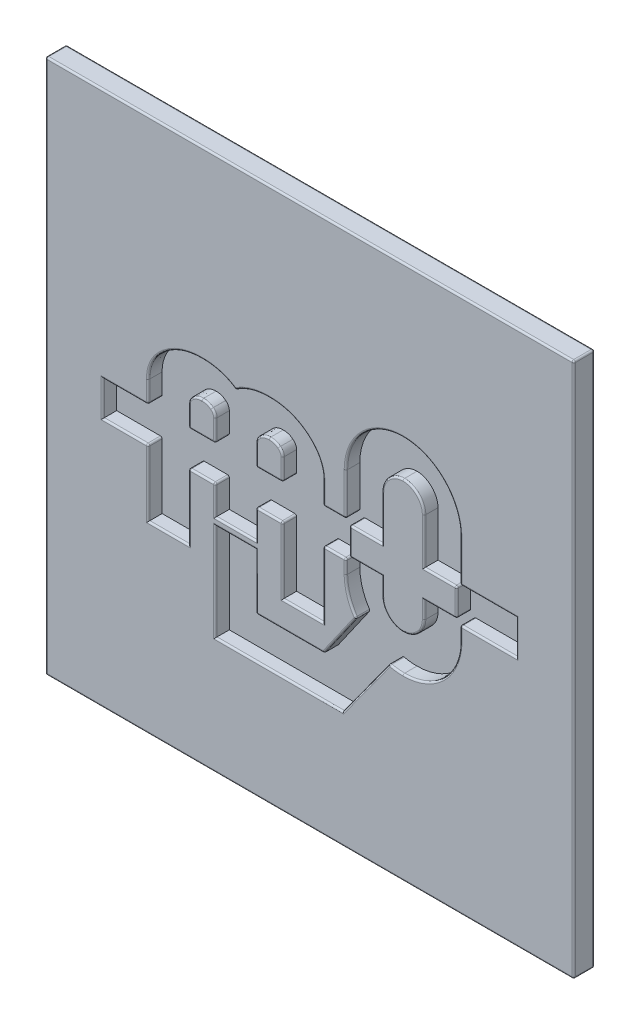
SolidWorks part; units mm, degrees
material "ABS"
ref_plane "Plano frontal" through (0, 0, 0) normal (0, 0, 1) x (1, 0, 0)
ref_plane "Plano superior" through (0, 0, 0) normal (0, 1, 0) x (1, 0, 0)
ref_plane "Plano direito" through (0, 0, 0) normal (1, 0, 0) x (0, 0, -1)
sketch "Model" plane through (0, 0, 0) normal (0, 0, 1) x (1, 0, 0)
  line L0 (10.7309, -25.7678) -> (10.7309, -42.8732)
  line L1 (10.7309, -42.8732) -> (15.5406, -42.8732)
  line L2 (15.5406, -42.8732) -> (15.5406, -25.7678)
  line L3 (20.3712, -25.7678) -> (20.3712, -37.5277)
  line L4 (20.3712, -37.5277) -> (25.1993, -37.5277)
  line L5 (25.1993, -37.5277) -> (25.1993, -25.7678)
  line L6 (30.03, -25.7678) -> (30.03, -42.8732)
  line L7 (30.03, -42.8732) -> (34.8396, -42.8732)
  line L8 (34.8396, -42.8732) -> (34.8396, -25.7678)
  line L9 (39.1028, -22.8429) -> (39.1028, -29.3604)
  line L10 (39.1028, -29.3604) -> (43.7804, -29.3604)
  line L11 (43.7804, -29.3604) -> (43.7804, -22.8429)
  line L12 (49.8174, -22.8429) -> (49.8174, -29.3604)
  line L13 (49.8174, -29.3604) -> (54.495, -29.3604)
  line L14 (54.495, -29.3604) -> (54.495, -22.8429)
  line L15 (43.7804, -35.841) -> (43.7804, -33.3385)
  line L16 (43.7804, -33.3385) -> (39.1028, -33.3385)
  line L17 (39.1028, -33.3385) -> (39.1028, -35.841)
  line L18 (54.495, -35.841) -> (54.495, -33.3385)
  line L19 (54.495, -33.3385) -> (49.8174, -33.3385)
  line L20 (49.8174, -33.3385) -> (49.8174, -35.841)
  line L21 (39.1028, -29.3604) -> (39.1028, -33.3385)
  line L22 (39.1028, -33.3385) -> (4.2108, -33.3385)
  line L23 (4.2108, -33.3385) -> (4.2108, -29.3604)
  line L24 (4.2108, -29.3604) -> (39.1028, -29.3604)
  line L25 (62.5568, -29.3604) -> (62.5568, -33.3385)
  line L26 (62.5568, -33.3385) -> (54.495, -33.3385)
  line L27 (54.495, -33.3385) -> (54.495, -29.3604)
  line L28 (54.495, -29.3604) -> (62.5568, -29.3604)
  line L29 (47.9644, -38.6153) -> (44.6225, -43.2216)
  line L30 (44.6225, -43.2216) -> (37.8938, -52.503)
  line L31 (37.8938, -52.503) -> (20.3712, -52.5003)
  line L32 (20.3712, -52.5003) -> (20.3712, -39.5946)
  line L33 (20.3712, -39.5946) -> (25.1888, -39.5946)
  line L34 (25.1888, -39.5946) -> (25.1888, -47.6142)
  line L35 (25.1888, -47.6142) -> (35.716, -47.6142)
  line L36 (35.716, -47.6142) -> (40.6893, -40.508)
  line L37 (40.6893, -40.508) -> (43.791, -36.0759)
  line L38 (47.9644, -38.6153) -> (44.6225, -43.2216)
  line L39 (40.6893, -40.508) -> (43.791, -36.0759)
  line L40 (25.2002, -33.3389) -> (20.3706, -33.3389)
  line L41 (20.3706, -33.3389) -> (20.3706, -29.3615)
  line L42 (20.3706, -29.3615) -> (25.2002, -29.3615)
  line L43 (25.2002, -29.3615) -> (25.2002, -33.3389)
  line L44 (4.2108, -31.3495) -> (62.5568, -31.3495) construction
  line L50 (-4.5162, -69.7495) -> (71.2838, -69.7495)
  line L51 (-4.5162, -69.7495) -> (-4.5162, 7.0505)
  line L52 (-4.5162, 7.0505) -> (71.2838, 7.0505)
  line L53 (71.2838, -69.7495) -> (71.2838, 7.0505)
  line L54 (-4.5162, -69.7495) -> (71.2838, 7.0505) construction
  line L55 (-4.5162, 7.0505) -> (71.2838, -69.7495) construction
  spline S0 degree 3 poles (32.7226, -21.5653) (31.3129, -20.4065) (29.605, -19.8257) (27.6041, -19.8257) knots 0 0 0 0 1 1 1 1
  spline S1 degree 3 poles (27.6041, -19.8257) (25.751, -19.8257) (24.1408, -20.3325) (22.7761, -21.3436) knots 1 1 1 1 2 2 2 2
  spline S2 degree 3 poles (22.7761, -21.3436) (21.4245, -20.3325) (19.8196, -19.8257) (17.9665, -19.8257) knots 2 2 2 2 3 3 3 3
  spline S3 degree 3 poles (17.9665, -19.8257) (15.9655, -19.8257) (14.255, -20.4091) (12.8375, -21.5732) knots 3 3 3 3 4 4 4 4
  spline S4 degree 3 poles (12.8375, -21.5732) (11.4332, -22.7268) (10.7309, -24.1232) (10.7309, -25.7678) knots 4 4 4 4 5 5 5 5
  spline S5 degree 3 poles (15.5406, -25.7678) (15.5406, -25.2213) (15.7755, -24.7567) (16.2454, -24.3713) knots 8 8 8 8 9 9 9 9
  spline S6 degree 3 poles (16.2454, -24.3713) (16.7179, -23.9859) (17.2907, -23.7906) (17.9665, -23.7906) knots 9 9 9 9 10 10 10 10
  spline S7 degree 3 poles (17.9665, -23.7906) (18.6291, -23.7906) (19.1992, -23.9833) (19.6744, -24.3634) knots 10 10 10 10 11 11 11 11
  spline S8 degree 3 poles (19.6744, -24.3634) (20.139, -24.7541) (20.3712, -25.2213) (20.3712, -25.7678) knots 11 11 11 11 12 12 12 12
  spline S9 degree 3 poles (25.1993, -25.7678) (25.1993, -25.2213) (25.4343, -24.7567) (25.9068, -24.3713) knots 15 15 15 15 16 16 16 16
  spline S10 degree 3 poles (25.9068, -24.3713) (26.3766, -23.9859) (26.9416, -23.7906) (27.6041, -23.7906) knots 16 16 16 16 17 17 17 17
  spline S11 degree 3 poles (27.6041, -23.7906) (28.2799, -23.7906) (28.8501, -23.9833) (29.3147, -24.3634) knots 17 17 17 17 18 18 18 18
  spline S12 degree 3 poles (29.3147, -24.3634) (29.7925, -24.7541) (30.03, -25.2213) (30.03, -25.7678) knots 18 18 18 18 19 19 19 19
  spline S13 degree 3 poles (34.8396, -25.7678) (34.8396, -24.1232) (34.1348, -22.7241) (32.7226, -21.5653) knots 22 22 22 22 23 23 23 23
  spline S14 degree 3 poles (46.7976, -15.1455) (42.5688, -15.1455) (39.1028, -18.6114) (39.1028, -22.8429) knots 0 0 0 0 1 1 1 1
  spline S15 degree 3 poles (43.7804, -22.8429) (43.7804, -21.2089) (45.1636, -19.8257) (46.7976, -19.8257) knots 4 4 4 4 5 5 5 5
  spline S16 degree 3 poles (46.7976, -19.8257) (48.4369, -19.8257) (49.8174, -21.2089) (49.8174, -22.8429) knots 5 5 5 5 6 6 6 6
  spline S17 degree 3 poles (54.495, -22.8429) (54.495, -18.6114) (51.0344, -15.1455) (46.7976, -15.1455) knots 9 9 9 9 10 10 10 10
  spline S18 degree 3 poles (49.8174, -35.841) (49.8174, -36.4877) (49.6036, -37.0922) (49.242, -37.5858) knots 0 0 0 0 1 1 1 1
  spline S19 degree 3 poles (49.242, -37.5858) (48.9173, -38.0346) (48.4765, -38.3962) (47.9644, -38.6153) knots 1 1 1 1 2 2 2 2
  spline S20 degree 3 poles (47.9644, -38.6153) (47.6054, -38.7737) (47.2094, -38.8608) (46.7976, -38.8608) knots 2 2 2 2 3 3 3 3
  spline S21 degree 3 poles (46.7976, -38.8608) (45.2402, -38.8608) (43.915, -37.6096) (43.791, -36.0759) knots 3 3 3 3 4 4 4 4
  spline S22 degree 3 poles (43.791, -36.0759) (43.783, -35.9994) (43.7804, -35.9175) (43.7804, -35.841) knots 4 4 4 4 5 5 5 5
  spline S23 degree 3 poles (39.1028, -35.841) (39.1028, -37.5885) (39.6941, -39.2119) (40.6893, -40.508) knots 8 8 8 8 9 9 9 9
  spline S24 degree 3 poles (40.6893, -40.508) (41.6686, -41.7883) (43.0413, -42.7544) (44.6225, -43.2216) knots 9 9 9 9 10 10 10 10
  spline S25 degree 3 poles (44.6225, -43.2216) (45.3141, -43.4275) (46.0426, -43.5384) (46.7976, -43.5384) knots 10 10 10 10 11 11 11 11
  spline S26 degree 3 poles (46.7976, -43.5384) (50.4325, -43.5384) (53.4999, -40.9884) (54.2918, -37.5858) knots 11 11 11 11 12 12 12 12
  spline S27 degree 3 poles (54.2918, -37.5858) (54.4264, -37.0235) (54.495, -36.4402) (54.495, -35.841) knots 12 12 12 12 13 13 13 13
  spline S28 degree 3 poles (43.791, -36.0759) (43.915, -37.6096) (45.2402, -38.8608) (46.7976, -38.8608) knots 9 9 9 9 10 10 10 10
  spline S29 degree 3 poles (46.7976, -38.8608) (47.2094, -38.8608) (47.6054, -38.7737) (47.9644, -38.6153) knots 10 10 10 10 11 11 11 11
  spline S30 degree 3 poles (44.6225, -43.2216) (43.0413, -42.7544) (41.6686, -41.7883) (40.6893, -40.508) knots 1 1 1 1 2 2 2 2
  spline S31 degree 3 poles (43.791, -36.0759) (43.915, -37.6096) (45.2402, -38.8608) (46.7976, -38.8608) knots 3 3 3 3 4 4 4 4
  spline S32 degree 3 poles (46.7976, -38.8608) (47.2094, -38.8608) (47.6054, -38.7737) (47.9644, -38.6153) knots 4 4 4 4 5 5 5 5
  point P63 (33.3838, -31.3495)
  dimension "D1" = 76.8
  dimension "D2" = 75.8
sketch "Esboço4" plane through (0, 0, 0) normal (0, 0, 1) x (1, 0, 0)
  line L1 (-4.5162, 7.0505) -> (71.2838, 7.0505)
  line L2 (-4.5162, 7.0505) -> (-4.5162, -69.7495)
  line L3 (-4.5162, -69.7495) -> (71.2838, -69.7495)
  line L4 (71.2838, 7.0505) -> (71.2838, -69.7495)
  point P4 (-4.5162, 7.0505)
  point P6 (71.2838, -69.7495)
extrude "Ressalto-extrusão6" add sketch "Esboço4" along normal blind 1 separate body
sketch "Esboço2" plane through (0, 0, 0) normal (0, 0, 1) x (1, 0, 0)
  line L0 (20.3706, -29.3615) -> (15.5406, -29.3604)
  line L1 (15.5406, -42.8732) -> (15.5406, -25.7678) construction
  line L2 (4.2108, -29.3604) -> (39.1028, -29.3604) construction
  line L3 (15.5406, -29.3604) -> (15.5406, -25.7678)
  line L4 (39.1028, -29.3604) -> (39.1028, -33.3385)
  line L5 (39.1028, -29.3604) -> (39.1028, -22.8429)
  line L6 (54.495, -33.3385) -> (62.5568, -33.3385)
  line L7 (62.5568, -33.3385) -> (62.5568, -29.3604)
  line L8 (62.5568, -29.3604) -> (54.495, -29.3604)
  line L9 (54.495, -33.3385) -> (54.495, -35.841)
  line L10 (44.6225, -43.2216) -> (37.8938, -52.503)
  line L11 (37.8938, -52.503) -> (20.3712, -52.5003)
  line L12 (20.3712, -52.5003) -> (20.3712, -39.5946)
  line L14 (-4.5162, 7.0505) -> (71.2838, 7.0505)
  line L15 (-4.5162, 7.0505) -> (-4.5162, -69.7495)
  line L16 (-4.5162, -69.7495) -> (71.2838, -69.7495)
  line L17 (71.2838, 7.0505) -> (71.2838, -69.7495)
  line L21 (16.0406, -28.8605) -> (16.0406, -25.7678)
  line L22 (19.8712, -25.7677) -> (19.8707, -28.8614)
  line L23 (19.8707, -28.8614) -> (16.0406, -28.8605)
  line L24 (25.6993, -25.7677) -> (25.7001, -28.8614)
  line L25 (-4.5162, 7.0505) -> (-4.5162, -69.7495)
  line L26 (-4.5162, -69.7495) -> (71.2838, -69.7495)
  line L27 (71.2838, -69.7495) -> (71.2838, 7.0505)
  line L28 (71.2838, 7.0505) -> (-4.5162, 7.0505)
  line L29 (-4.5162, 7.0505) -> (-4.5162, -69.7495)
  line L30 (-4.5162, -69.7495) -> (71.2838, -69.7495)
  line L31 (71.2838, -69.7495) -> (71.2838, 7.0505)
  line L32 (71.2838, 7.0505) -> (-4.5162, 7.0505)
  line L33 (25.7001, -28.8614) -> (29.53, -28.8605)
  line L34 (29.53, -28.8605) -> (29.53, -25.7678)
  line L35 (39.6028, -32.8385) -> (44.2804, -32.8385)
  line L36 (44.2804, -33.3385) -> (44.2804, -35.841)
  line L37 (49.3174, -35.841) -> (49.3174, -32.8385)
  line L38 (49.3174, -32.8385) -> (53.995, -32.8385)
  line L39 (53.995, -32.8385) -> (53.995, -29.8604)
  line L40 (53.995, -29.8604) -> (49.3174, -29.8604)
  line L41 (49.3174, -29.8604) -> (49.3174, -22.8429)
  line L42 (44.2804, -22.8429) -> (44.2804, -29.8604)
  line L43 (44.2804, -29.8604) -> (39.6028, -29.8604)
  line L44 (39.6028, -29.8604) -> (39.6028, -32.8385)
  line L45 (38.6028, -33.3385) -> (38.6028, -35.841)
  line L46 (40.0744, -40.5146) -> (35.4557, -47.1142)
  line L47 (35.4557, -47.1142) -> (25.6888, -47.1142)
  line L48 (25.6888, -47.1142) -> (25.6888, -39.0946)
  line L49 (19.8712, -39.0946) -> (25.6888, -39.0946)
  line L50 (19.8712, -53.0002) -> (19.8712, -39.0946)
  line L51 (38.1489, -53.003) -> (19.8712, -53.0002)
  line L52 (44.8242, -43.7952) -> (38.1489, -53.003)
  line L53 (54.995, -33.8385) -> (54.995, -35.841)
  line L54 (54.995, -33.8385) -> (63.0568, -33.8385)
  line L55 (63.0568, -33.8385) -> (63.0568, -28.8604)
  line L56 (63.0568, -28.8604) -> (54.995, -28.8604)
  line L57 (54.995, -22.8429) -> (54.995, -28.8604)
  line L58 (38.6028, -28.8604) -> (38.6028, -22.8429)
  line L59 (35.3396, -28.8604) -> (38.6028, -28.8604)
  line L60 (35.3396, -25.7678) -> (35.3396, -28.8604)
  line L61 (10.2309, -25.7678) -> (10.2309, -28.8604)
  line L62 (3.7108, -28.8604) -> (10.2309, -28.8604)
  line L63 (3.7108, -33.8385) -> (3.7108, -28.8604)
  line L64 (10.2309, -33.8385) -> (3.7108, -33.8385)
  line L65 (10.2309, -43.3732) -> (10.2309, -33.8385)
  line L66 (16.0406, -43.3732) -> (10.2309, -43.3732)
  line L67 (16.0406, -33.8385) -> (16.0406, -43.3732)
  line L68 (19.8707, -33.8389) -> (16.0406, -33.8385)
  line L69 (19.8713, -38.0277) -> (19.8707, -33.8389)
  line L70 (25.6992, -38.0277) -> (19.8713, -38.0277)
  line L71 (25.6992, -38.0277) -> (25.7001, -33.8389)
  line L72 (25.7001, -33.8389) -> (29.53, -33.8385)
  line L73 (29.53, -33.8385) -> (29.53, -43.3732)
  line L74 (29.53, -43.3732) -> (35.3396, -43.3732)
  line L75 (35.3396, -43.3732) -> (35.3396, -33.8385)
  line L76 (35.3396, -33.8385) -> (39.1028, -33.8385)
  line L77 (39.6028, -29.8604) -> (39.6028, -33.3385) construction
  line L78 (39.1028, -32.8385) -> (44.2804, -32.8385) construction
  line L79 (44.2804, -32.8385) -> (44.2804, -35.841) construction
  line L80 (44.2804, -33.3385) -> (44.2804, -32.8385)
  line L189 (20.3712, -25.7678) -> (20.3706, -29.3615)
  line L190 (25.2002, -29.3615) -> (30.03, -29.3604)
  line L191 (30.03, -25.7678) -> (30.03, -42.8732) construction
  line L192 (30.03, -29.3604) -> (30.03, -25.7678)
  line L193 (25.1993, -25.7678) -> (25.2002, -29.3615)
  line L194 (20.3712, -37.5277) -> (20.3712, -39.5946) construction
  line L195 (20.3712, -39.5946) -> (25.1888, -39.5946)
  line L196 (25.1888, -39.5946) -> (25.1993, -37.5277) construction
  line L197 (25.1993, -37.5277) -> (20.3712, -37.5277)
  line L198 (25.1993, -37.5277) -> (25.2002, -33.3389)
  line L199 (43.7804, -22.8429) -> (43.7804, -29.3604)
  line L200 (49.8174, -29.3604) -> (49.8174, -22.8429)
  line L201 (54.495, -29.3604) -> (49.8174, -29.3604)
  line L202 (54.495, -33.3385) -> (54.495, -29.3604)
  line L203 (49.8174, -33.3385) -> (54.495, -33.3385)
  line L204 (49.8174, -35.841) -> (49.8174, -33.3385)
  line L205 (43.7804, -33.3385) -> (43.7804, -35.841)
  line L206 (39.1028, -33.3385) -> (43.7804, -33.3385)
  line L207 (39.1028, -29.3604) -> (39.1028, -33.3385)
  line L208 (43.7804, -29.3604) -> (39.1028, -29.3604)
  line L209 (43.7804, -22.8429) -> (43.7804, -29.3604)
  line L210 (49.8174, -29.3604) -> (49.8174, -22.8429)
  line L211 (54.495, -29.3604) -> (49.8174, -29.3604)
  line L212 (54.495, -33.3385) -> (54.495, -29.3604)
  line L213 (49.8174, -33.3385) -> (54.495, -33.3385)
  line L214 (49.8174, -35.841) -> (49.8174, -33.3385)
  line L215 (43.7804, -33.3385) -> (43.7804, -35.841)
  line L216 (39.1028, -33.3385) -> (43.7804, -33.3385)
  line L217 (39.1028, -29.3604) -> (39.1028, -33.3385) construction
  line L218 (43.7804, -29.3604) -> (39.1028, -29.3604)
  line L219 (25.2002, -33.3389) -> (30.03, -33.3385)
  line L220 (39.1028, -33.3385) -> (4.2108, -33.3385) construction
  line L221 (30.03, -33.3385) -> (30.03, -42.8732)
  line L222 (30.03, -42.8732) -> (34.8396, -42.8732)
  line L223 (34.8396, -42.8732) -> (34.8396, -33.3385)
  line L224 (34.8396, -42.8732) -> (34.8396, -25.7678) construction
  line L225 (34.8396, -33.3385) -> (39.1028, -33.3385)
  line L226 (40.6893, -40.508) -> (35.716, -47.6142)
  line L227 (35.716, -47.6142) -> (25.1888, -47.6142)
  line L228 (25.1888, -47.6142) -> (25.1888, -39.5946)
  line L230 (20.3712, -37.5277) -> (20.3706, -33.3389)
  line L231 (39.1028, -33.3385) -> (39.1028, -35.841)
  line L232 (39.1028, -33.3385) -> (39.1028, -35.841)
  line L233 (20.3706, -33.3389) -> (15.5406, -33.3385)
  line L234 (15.5406, -33.3385) -> (15.5406, -42.8732)
  line L235 (15.5406, -42.8732) -> (10.7309, -42.8732)
  line L236 (10.7309, -42.8732) -> (10.7309, -33.3385)
  line L237 (10.7309, -25.7678) -> (10.7309, -42.8732) construction
  line L238 (10.7309, -33.3385) -> (4.2108, -33.3385)
  line L239 (4.2108, -33.3385) -> (4.2108, -29.3604)
  line L240 (4.2108, -29.3604) -> (10.7309, -29.3604)
  line L241 (10.7309, -25.7678) -> (10.7309, -29.3604)
  line L242 (34.8396, -25.7678) -> (34.8396, -29.3604)
  line L243 (34.8396, -29.3604) -> (39.1028, -29.3604)
  line L244 (54.495, -22.8429) -> (54.495, -29.3604)
  spline S0 degree 1 poles (16.0406, -25.7678) (16.5619, -24.7584) knots 0 0 1 1 construction
  spline S1 degree 1 poles (16.5619, -24.7584) (17.9665, -24.2906) knots 0 0 1 1 construction
  spline S2 degree 1 poles (17.9665, -24.2906) (19.3573, -24.75) knots 0 0 1 1 construction
  spline S3 degree 1 poles (19.3573, -24.75) (19.8712, -25.7677) knots 0 0 1 1 construction
  spline S4 degree 3 poles (16.0406, -25.7678) (16.0406, -25.6734) (16.0617, -25.4788) (16.153, -25.2331) (16.3041, -24.9973) (16.4751, -24.8296) (16.5619, -24.7584) knots 8 8 8 8 8.249884 8.499767 8.749651 8.999535 8.999535 8.999535 8.999535
  spline S5 degree 3 poles (16.5619, -24.7584) (16.6555, -24.6821) (16.8576, -24.5445) (17.1847, -24.401) (17.5451, -24.3114) (17.8293, -24.2906) (17.9665, -24.2906) knots 9.000463 9.000463 9.000463 9.000463 9.250347 9.500232 9.750116 10 10 10 10
  spline S6 degree 3 poles (17.9665, -24.2906) (18.1005, -24.2906) (18.3773, -24.3109) (18.7336, -24.3986) (19.0598, -24.5397) (19.263, -24.675) (19.3573, -24.75) knots 10 10 10 10 10.24897 10.49794 10.74691 10.99588 10.99588 10.99588 10.99588
  spline S7 degree 3 poles (19.3573, -24.75) (19.4428, -24.8224) (19.6106, -24.9915) (19.76, -25.2299) (19.8504, -25.4781) (19.8712, -25.6731) (19.8712, -25.7677) knots 11.004142 11.004142 11.004142 11.004142 11.253098 11.502054 11.75101 11.999967 11.999967 11.999967 11.999967
  spline S8 degree 3 poles (4271.8577, -4273.494) (-3645.8779, 4797.7366) (3079.4597, -5303.5344) (-2255.9005, 5478.3498) knots -61.185451 -61.185451 -61.185451 -61.185451 75.014318 75.014318 75.014318 75.014318 only from (44.6225, -43.2216) to (46.7976, -43.5384)
  spline S9 degree 3 poles (728.2813, 5865.8985) (-1979.4806, -5530.0237) (3297.6048, 4845.785) (-4259.162, -4136.3012) knots -89.295263 -89.295263 -89.295263 -89.295263 109.691124 109.691124 109.691124 109.691124 only from (54.2918, -37.5858) to (54.495, -35.841)
  spline S10 degree 3 poles (3344.1938, 4945.5493) (-3941.8044, -4582.4964) (4618.0367, 3924.9483) (-4955.1804, -3303.294) knots -1.968852 -1.968852 -1.968852 -1.968852 25.128151 25.128151 25.128151 25.128151 only from (46.7976, -43.5384) to (54.2918, -37.5858)
  spline S11 degree 3 poles (44.6225, -43.2216) (45.3141, -43.4275) (46.0426, -43.5384) (46.7976, -43.5384) knots 10 10 10 10 11 11 11 11
  spline S12 degree 3 poles (54.2918, -37.5858) (54.4264, -37.0235) (54.495, -36.4402) (54.495, -35.841) knots 12 12 12 12 13 13 13 13
  spline S13 degree 3 poles (46.7976, -43.5384) (50.4325, -43.5384) (53.4999, -40.9884) (54.2918, -37.5858) knots 11 11 11 11 12 12 12 12
  spline S14 degree 1 poles (28.9981, -24.7504) (29.53, -25.7678) knots 0 0 1 1 construction
  spline S15 degree 1 poles (27.6041, -24.2906) (28.9981, -24.7504) knots 0 0 1 1 construction
  spline S16 degree 1 poles (26.2233, -24.7584) (27.6041, -24.2906) knots 0 0 1 1 construction
  spline S17 degree 1 poles (25.6993, -25.7677) (26.2233, -24.7584) knots 0 0 1 1 construction
  spline S18 degree 3 poles (29.53, -25.7678) (29.53, -25.6736) (29.5088, -25.4796) (29.4162, -25.2326) (29.2621, -24.994) (29.0869, -24.823) (28.9981, -24.7504) knots 17.999964 17.999964 17.999964 17.999964 18.249973 18.499982 18.749991 19 19 19 19
  spline S19 degree 3 poles (28.9981, -24.7504) (28.9066, -24.6755) (28.7091, -24.5411) (28.3854, -24.3996) (28.0264, -24.3113) (27.7415, -24.2906) (27.6041, -24.2906) knots 17 17 17 17 17.250009 17.500019 17.750028 18.000037 18.000037 18.000037 18.000037
  spline S20 degree 3 poles (27.6041, -24.2906) (27.4703, -24.2906) (27.1933, -24.3113) (26.84, -24.4005) (26.5178, -24.5436) (26.3164, -24.6821) (26.2233, -24.7584) knots 15.999619 15.999619 15.999619 15.999619 16.249714 16.499809 16.749905 17 17 17 17
  spline S21 degree 3 poles (26.2233, -24.7584) (26.1359, -24.8296) (25.9636, -24.9976) (25.812, -25.2332) (25.7205, -25.4786) (25.6993, -25.6734) (25.6993, -25.7677) knots 15.000046 15.000046 15.000046 15.000046 15.25013 15.500213 15.750297 16.00038 16.00038 16.00038 16.00038
  spline S22 degree 1 poles (44.2893, -36.0356) (46.7976, -38.3608) knots 0 0 1 1 construction
  spline S23 degree 1 poles (46.7976, -38.3608) (47.7651, -38.1567) knots 0 0 1 1 construction
  spline S24 degree 1 poles (47.7651, -38.1567) (48.8378, -37.2916) knots 0 0 1 1 construction
  spline S25 degree 1 poles (48.8378, -37.2916) (49.3174, -35.841) knots 0 0 1 1 construction
  spline S26 degree 1 poles (49.3174, -22.8429) (46.7976, -20.3257) knots 0 0 1 1 construction
  spline S27 degree 1 poles (46.7976, -20.3257) (44.2804, -22.8429) knots 0 0 1 1 construction
  spline S28 degree 3 poles (44.2893, -36.0356) (44.3144, -36.3459) (44.4904, -36.9638) (45.0612, -37.7175) (45.8506, -38.2323) (46.485, -38.3608) (46.7976, -38.3608) knots 3 3 3 3 3.25 3.5 3.75 4 4 4 4
  spline S29 degree 3 poles (46.7976, -38.3608) (46.8823, -38.3608) (47.0527, -38.3518) (47.2991, -38.3123) (47.5379, -38.2482) (47.6904, -38.1897) (47.7651, -38.1567) knots 2 2 2 2 2.250601 2.501202 2.751803 3.002404 3.002404 3.002404 3.002404
  spline S30 degree 3 poles (47.7651, -38.1567) (47.8715, -38.1112) (48.0783, -38.0051) (48.3631, -37.8046) (48.6198, -37.567) (48.7693, -37.3862) (48.8378, -37.2916) knots 0.998307 0.998307 0.998307 0.998307 1.248951 1.499594 1.750238 2.000882 2.000882 2.000882 2.000882
  spline S31 degree 3 poles (48.8378, -37.2916) (48.9134, -37.1884) (49.0493, -36.9705) (49.2006, -36.6157) (49.2953, -36.2398) (49.3174, -35.973) (49.3174, -35.841) knots -0.000798 -0.000798 -0.000798 -0.000798 0.249401 0.499601 0.7498 1 1 1 1
  spline S32 degree 3 poles (49.3174, -22.8429) (49.3174, -22.5151) (49.1758, -21.85) (48.6107, -21.0332) (47.7938, -20.4678) (47.1263, -20.3257) (46.7976, -20.3257) knots 5 5 5 5 5.25 5.5 5.75 6 6 6 6
  spline S33 degree 3 poles (46.7976, -20.3257) (46.4699, -20.3257) (45.805, -20.4676) (44.9879, -21.0332) (44.4223, -21.8503) (44.2804, -22.5152) (44.2804, -22.8429) knots 4 4 4 4 4.25 4.5 4.75 5 5 5 5
  spline S34 degree 1 poles (38.6028, -35.841) (40.0744, -40.5146) knots 0 0 1 1 construction
  spline S35 degree 1 poles (44.8242, -43.7952) (46.7976, -44.0384) knots 0 0 1 1 construction
  spline S36 degree 1 poles (46.7976, -44.0384) (54.7784, -37.7007) knots 0 0 1 1 construction
  spline S37 degree 1 poles (54.7784, -37.7007) (54.995, -35.841) knots 0 0 1 1 construction
  spline S38 degree 1 poles (54.995, -22.8429) (46.7976, -14.6455) knots 0 0 1 1 construction
  spline S39 degree 1 poles (46.7976, -14.6455) (38.6028, -22.8429) knots 0 0 1 1 construction
  spline S40 degree 1 poles (35.3396, -25.7678) (33.0399, -21.1789) knots 0 0 1 1 construction
  spline S41 degree 1 poles (33.0399, -21.1789) (27.6041, -19.3257) knots 0 0 1 1 construction
  spline S42 degree 1 poles (27.6041, -19.3257) (22.7774, -20.7304) knots 0 0 1 1 construction
  spline S43 degree 1 poles (22.7774, -20.7304) (17.9665, -19.3257) knots 0 0 1 1 construction
  spline S44 degree 1 poles (17.9665, -19.3257) (12.5201, -21.1868) knots 0 0 1 1 construction
  spline S45 degree 1 poles (12.5201, -21.1868) (10.2309, -25.7678) knots 0 0 1 1 construction
  spline S46 degree 3 poles (38.6028, -35.841) (38.6028, -36.2666) (38.6708, -37.127) (38.9618, -38.3404) (39.4271, -39.4836) (39.842, -40.1819) (40.0744, -40.5146) knots 8 8 8 8 8.232322 8.464643 8.696965 8.929287 8.929287 8.929287 8.929287
  spline S47 degree 3 poles (44.8242, -43.7952) (44.983, -43.835) (45.3021, -43.9049) (45.7922, -43.9813) (46.2897, -44.0279) (46.6288, -44.0384) (46.7976, -44.0384) knots 10.154566 10.154566 10.154566 10.154566 10.365924 10.577283 10.788641 11 11 11 11
  spline S48 degree 3 poles (46.7976, -44.0384) (47.2727, -44.0384) (48.2341, -43.9535) (50.023, -43.4727) (52.0199, -42.3385) (53.8396, -40.3149) (54.5717, -38.588) (54.7784, -37.7007) knots 11 11 11 11 11.124982 11.249965 11.499929 11.749894 11.999858 11.999858 11.999858 11.999858
  spline S49 degree 3 poles (54.7784, -37.7007) (54.8144, -37.5503) (54.8773, -37.2478) (54.9451, -36.7854) (54.9859, -36.3172) (54.995, -35.9993) (54.995, -35.841) knots 12.000855 12.000855 12.000855 12.000855 12.250641 12.500427 12.750214 13 13 13 13
  spline S50 degree 3 poles (54.995, -22.8429) (54.995, -22.2913) (54.8799, -21.173) (54.2328, -19.1241) (52.7306, -16.9123) (50.5191, -15.4087) (48.4693, -14.7608) (47.3498, -14.6455) (46.7976, -14.6455) knots 9 9 9 9 9.125 9.25 9.5 9.75 9.875 10 10 10 10
  spline S51 degree 3 poles (46.7976, -14.6455) (46.2462, -14.6455) (45.1284, -14.7608) (43.0803, -15.4088) (40.8692, -16.9122) (39.366, -19.124) (38.7181, -21.1728) (38.6028, -22.2912) (38.6028, -22.8429) knots 0 0 0 0 0.125 0.25 0.5 0.75 0.875 1 1 1 1
  spline S52 degree 3 poles (35.3396, -25.7678) (35.3396, -25.3317) (35.2442, -24.4477) (34.8032, -23.2407) (34.0867, -22.1466) (33.4, -21.4745) (33.0399, -21.1789) knots 22 22 22 22 22.24999 22.49998 22.74997 22.99996 22.99996 22.99996 22.99996
  spline S53 degree 3 poles (33.0399, -21.1789) (32.6697, -20.8746) (31.8715, -20.3276) (30.5631, -19.7489) (29.1512, -19.4017) (28.1132, -19.3257) (27.6041, -19.3257) knots 0.00004 0.00004 0.00004 0.00004 0.25003 0.50002 0.75001 1 1 1 1
  spline S54 degree 3 poles (27.6041, -19.3257) (27.1621, -19.3257) (26.2635, -19.3834) (25.02, -19.6463) (23.849, -20.0851) (23.1221, -20.498) (22.7774, -20.7304) knots 1 1 1 1 1.233058 1.466117 1.699175 1.932234 1.932234 1.932234 1.932234
  spline S55 degree 3 poles (22.7774, -20.7304) (22.4351, -20.4978) (21.7131, -20.085) (20.5466, -19.6461) (19.3062, -19.3834) (18.4081, -19.3257) (17.9665, -19.3257) knots 2.068142 2.068142 2.068142 2.068142 2.301106 2.534071 2.767035 3 3 3 3
  spline S56 degree 3 poles (17.9665, -19.3257) (17.4571, -19.3257) (16.4187, -19.4021) (15.0048, -19.751) (13.6935, -20.332) (12.8919, -20.8815) (12.5201, -21.1868) knots 3 3 3 3 3.250001 3.500003 3.750004 4.000005 4.000005 4.000005 4.000005
  spline S57 degree 3 poles (12.5201, -21.1868) (12.1616, -21.4814) (11.4785, -22.151) (10.7651, -23.243) (10.326, -24.4483) (10.2309, -25.3319) (10.2309, -25.7678) knots 3.999995 3.999995 3.999995 3.999995 4.249996 4.499997 4.749999 5 5 5 5
  spline S58 degree 1 poles (44.2804, -35.841) (44.2883, -36.0244) knots 0 0 1 1 construction
  spline S59 degree 3 poles (44.2804, -35.841) (44.2804, -35.8572) (44.2807, -35.8899) (44.2821, -35.9379) (44.2846, -35.9841) (44.2869, -36.0106) (44.2883, -36.0244) knots 4 4 4 4 4.25 4.5 4.75 5 5 5 5
  spline S335 degree 3 poles (-4720.9621, 3600.3277) (4489.0748, -4104.6904) (-3993.2429, 4457.4487) (3624.9042, -4824.4353) knots -10.05937 -10.05937 -10.05937 -10.05937 21.05483 21.05483 21.05483 21.05483 only from (49.8174, -22.8429) to (46.7976, -19.8257)
  spline S336 degree 3 poles (-3556.8982, -4805.1822) (4108.8845, 4437.8668) (-4413.8174, -4085.0809) (4829.1056, 3581.0506) knots -11.033288 -11.033288 -11.033288 -11.033288 20.033376 20.033376 20.033376 20.033376 only from (46.7976, -19.8257) to (43.7804, -22.8429)
  spline S337 degree 3 poles (3534.0198, 4833.9524) (-3921.9814, -4575.9403) (4437.4756, 4096.7984) (-4688.8574, -3699.9075) knots -40.034909 -40.034909 -40.034909 -40.034909 39.552739 39.552739 39.552739 39.552739 only from (49.242, -37.5858) to (49.8174, -35.841)
  spline S338 degree 3 poles (3131.6534, 5097.4652) (-3526.5104, -4898.7421) (4058.1287, 4472.9545) (-4333.1695, -4121.5813) knots -41.89627 -41.89627 -41.89627 -41.89627 45.746992 45.746992 45.746992 45.746992 only from (47.9644, -38.6153) to (49.242, -37.5858)
  spline S339 degree 3 poles (4262.2188, 4216.0421) (-4596.4914, -3875.5288) (5047.3348, 3326.6117) (-5226.9709, -2875.9016) knots -57.519532 -57.519532 -57.519532 -57.519532 64.519047 64.519047 64.519047 64.519047 only from (46.7976, -38.8608) to (47.9644, -38.6153)
  spline S340 degree 3 poles (4833.1636, -3634.6018) (-4414.9716, 4024.4097) (4107.0778, -4497.4629) (-3552.0921, 4750.0554) knots -12.888345 -12.888345 -12.888345 -12.888345 19.836352 19.836352 19.836352 19.836352 only from (43.791, -36.0759) to (46.7976, -38.8608)
  spline S341 degree 3 poles (-1337.0278, -5874.201) (1473.8272, 5815.7698) (-1436.3568, -5875.1472) (1574.8719, 5764.8353) knots -77.559627 -77.559627 -77.559627 -77.559627 86.381147 86.381147 86.381147 86.381147 only from (43.7804, -35.841) to (43.791, -36.0759)
  spline S342 degree 3 poles (49.8174, -22.8429) (49.8174, -21.2089) (48.4369, -19.8257) (46.7976, -19.8257) knots 5 5 5 5 6 6 6 6
  spline S343 degree 3 poles (46.7976, -19.8257) (45.1636, -19.8257) (43.7804, -21.2089) (43.7804, -22.8429) knots 4 4 4 4 5 5 5 5
  spline S344 degree 3 poles (49.242, -37.5858) (49.6036, -37.0922) (49.8174, -36.4877) (49.8174, -35.841) knots 0 0 0 0 1 1 1 1
  spline S345 degree 3 poles (47.9644, -38.6153) (48.4765, -38.3962) (48.9173, -38.0346) (49.242, -37.5858) knots 1 1 1 1 2 2 2 2
  spline S346 degree 3 poles (46.7976, -38.8608) (47.2094, -38.8608) (47.6054, -38.7737) (47.9644, -38.6153) knots 2 2 2 2 3 3 3 3
  spline S347 degree 3 poles (43.791, -36.0759) (43.915, -37.6096) (45.2402, -38.8608) (46.7976, -38.8608) knots 3 3 3 3 4 4 4 4
  spline S348 degree 3 poles (43.7804, -35.841) (43.7804, -35.9175) (43.783, -35.9994) (43.791, -36.0759) knots 4 4 4 4 5 5 5 5
  spline S355 degree 3 poles (-5943.7093, 174.5447) (1704.6453, -1303.9248) (1935.2976, 2331.3859) (-4897.6048, -3439.5761) knots -80.124792 -80.124792 -80.124792 -80.124792 96.341421 96.341421 96.341421 96.341421 only from (19.6744, -24.3634) to (20.3712, -25.7678)
  spline S356 degree 3 poles (-601.3216, -5959.9252) (-691.8875, 5183.2135) (2728.8089, -3362.5186) (-5572.5889, -368.7411) knots -67.522189 -67.522189 -67.522189 -67.522189 113.269581 113.269581 113.269581 113.269581 only from (17.9665, -23.7906) to (19.6744, -24.3634)
  spline S357 degree 3 poles (4944.8778, -3425.5488) (-1956.8315, 2320.5097) (-1611.0769, -1274.8692) (5982.1415, 104.5052) knots -75.628684 -75.628684 -75.628684 -75.628684 100.007768 100.007768 100.007768 100.007768 only from (15.5406, -25.7678) to (16.2454, -24.3713)
  spline S358 degree 3 poles (-1893.5271, 3493.9405) (3903.8854, -7894.7796) (-3685.2338, 7121.322) (2907.0343, -5280.8346) knots -133.304162 -133.304162 -133.304162 -133.304162 83.45877 83.45877 83.45877 83.45877 only from (16.2454, -24.3713) to (17.9665, -23.7906)
  spline S359 degree 3 poles (19.6744, -24.3634) (20.139, -24.7541) (20.3712, -25.2213) (20.3712, -25.7678) knots 11 11 11 11 12 12 12 12
  spline S360 degree 3 poles (17.9665, -23.7906) (18.6291, -23.7906) (19.1992, -23.9833) (19.6744, -24.3634) knots 10 10 10 10 11 11 11 11
  spline S361 degree 3 poles (15.5406, -25.7678) (15.5406, -25.2213) (15.7755, -24.7567) (16.2454, -24.3713) knots 8 8 8 8 9 9 9 9
  spline S362 degree 3 poles (16.2454, -24.3713) (16.7179, -23.9859) (17.2907, -23.7906) (17.9665, -23.7906) knots 9 9 9 9 10 10 10 10
  spline S370 degree 3 poles (4899.0215, -3520.7739) (-4347.1615, 4122.162) (3837.7229, -4752.3667) (-3042.065, 5083.5696) knots -18.756651 -18.756651 -18.756651 -18.756651 37.006092 37.006092 37.006092 37.006092 only from (39.1028, -35.841) to (40.6893, -40.508)
  spline S371 degree 3 poles (39.1028, -35.841) (39.1028, -37.5885) (39.6941, -39.2119) (40.6893, -40.508) knots 8 8 8 8 9 9 9 9
  spline S372 degree 3 poles (-5956.2416, -54.6879) (3614.2899, -908.9492) (-277.4055, 2253.1887) (-4025.584, -4341.9902) knots -61.535751 -61.535751 -61.535751 -61.535751 111.853647 111.853647 111.853647 111.853647 only from (29.3147, -24.3634) to (30.03, -25.7678)
  spline S373 degree 3 poles (-1940.6239, -5679.3698) (1381.2941, 6335.4992) (539.5637, -5643.8433) (-4727.2706, 1261.2846) knots -58.981814 -58.981814 -58.981814 -58.981814 141.962618 141.962618 141.962618 141.962618 only from (27.6041, -23.7906) to (29.3147, -24.3634)
  spline S374 degree 3 poles (3992.5203, -4421.151) (371.7388, 2281.1952) (-3570.4776, -894.4277) (6010.5566, -103.3339) knots -77.947154 -77.947154 -77.947154 -77.947154 95.739533 95.739533 95.739533 95.739533 only from (25.1993, -25.7678) to (25.9068, -24.3713)
  spline S375 degree 3 poles (-1763.0699, 3555.97) (3711.3675, -7969.0354) (-3503.4034, 7195.9561) (2795.7609, -5345.4547) knots -126.696056 -126.696056 -126.696056 -126.696056 90.833807 90.833807 90.833807 90.833807 only from (25.9068, -24.3713) to (27.6041, -23.7906)
  spline S376 degree 3 poles (29.3147, -24.3634) (29.7925, -24.7541) (30.03, -25.2213) (30.03, -25.7678) knots 18 18 18 18 19 19 19 19
  spline S377 degree 3 poles (27.6041, -23.7906) (28.2799, -23.7906) (28.8501, -23.9833) (29.3147, -24.3634) knots 17 17 17 17 18 18 18 18
  spline S378 degree 3 poles (25.1993, -25.7678) (25.1993, -25.2213) (25.4343, -24.7567) (25.9068, -24.3713) knots 15 15 15 15 16 16 16 16
  spline S379 degree 3 poles (25.9068, -24.3713) (26.3766, -23.9859) (26.9416, -23.7906) (27.6041, -23.7906) knots 16 16 16 16 17 17 17 17
  spline S403 degree 3 poles (-3242.6672, -5009.669) (4025.5709, 4533.3554) (-4513.3231, -3997.0278) (5036.8527, 3261.4409) knots -11.116491 -11.116491 -11.116491 -11.116491 12.116082 12.116082 12.116082 12.116082 only from (46.7976, -15.1455) to (39.1028, -22.8429)
  spline S404 degree 3 poles (-4933.8859, 3275.2785) (4593.5224, -4011.2237) (-3914.7562, 4547.3055) (3315.5886, -5022.904) knots -2.130825 -2.130825 -2.130825 -2.130825 21.127221 21.127221 21.127221 21.127221 only from (54.495, -22.8429) to (46.7976, -15.1455)
  spline S405 degree 3 poles (-5201.832, -2949.5858) (1518.7058, 1247.9905) (2269.7529, -1.6042) (-5885.0588, -1000.4174) knots -29.492725 -29.492725 -29.492725 -29.492725 73.258543 73.258543 73.258543 73.258543 only from (34.8396, -25.7678) to (32.7226, -21.5653)
  spline S406 degree 3 poles (-3301.5758, -4982.3105) (1925.081, 1264.7568) (-61.735, 2217.2074) (-2041.3177, -5627.2173) knots -54.749593 -54.749593 -54.749593 -54.749593 55.547614 55.547614 55.547614 55.547614 only from (32.7226, -21.5653) to (27.6041, -19.8257)
  spline S407 degree 3 poles (2253.4387, -5575.7761) (-233.1162, 2416.568) (-1488.5813, 1097.5549) (3069.2486, -5168.8106) knots -56.694107 -56.694107 -56.694107 -56.694107 62.487307 62.487307 62.487307 62.487307 only from (27.6041, -19.8257) to (22.7761, -21.3436)
  spline S408 degree 3 poles (-3413.7557, -4904.6357) (2050.1555, 1165.3918) (-249.1631, 2315.3235) (-1815.9946, -5702.6991) knots -56.793419 -56.793419 -56.793419 -56.793419 61.321149 61.321149 61.321149 61.321149 only from (22.7761, -21.3436) to (17.9665, -19.8257)
  spline S409 degree 3 poles (2455.2957, -5489.7257) (-390.0703, 2297.7925) (-1395.3157, 1206.527) (2985.9564, -5217.1253) knots -50.789883 -50.789883 -50.789883 -50.789883 59.968743 59.968743 59.968743 59.968743 only from (17.9665, -19.8257) to (12.8375, -21.5732)
  spline S410 degree 3 poles (5917.8783, -1073.7612) (-1737.1791, -52.1266) (-1970.31, 1292.6744) (5324.6887, -2809.7361) knots -48.018062 -48.018062 -48.018062 -48.018062 55.166724 55.166724 55.166724 55.166724 only from (12.8375, -21.5732) to (10.7309, -25.7678)
  spline S411 degree 3 poles (34.8396, -25.7678) (34.8396, -24.1232) (34.1348, -22.7241) (32.7226, -21.5653) knots 22 22 22 22 23 23 23 23
  spline S412 degree 3 poles (32.7226, -21.5653) (31.3129, -20.4065) (29.605, -19.8257) (27.6041, -19.8257) knots 0 0 0 0 1 1 1 1
  spline S413 degree 3 poles (27.6041, -19.8257) (25.751, -19.8257) (24.1408, -20.3325) (22.7761, -21.3436) knots 1 1 1 1 2 2 2 2
  spline S414 degree 3 poles (22.7761, -21.3436) (21.4245, -20.3325) (19.8196, -19.8257) (17.9665, -19.8257) knots 2 2 2 2 3 3 3 3
  spline S415 degree 3 poles (17.9665, -19.8257) (15.9655, -19.8257) (14.255, -20.4091) (12.8375, -21.5732) knots 3 3 3 3 4 4 4 4
  spline S416 degree 3 poles (12.8375, -21.5732) (11.4332, -22.7268) (10.7309, -24.1232) (10.7309, -25.7678) knots 4 4 4 4 5 5 5 5
  spline S417 degree 3 poles (46.7976, -15.1455) (42.5688, -15.1455) (39.1028, -18.6114) (39.1028, -22.8429) knots 0 0 0 0 1 1 1 1
  spline S418 degree 3 poles (54.495, -22.8429) (54.495, -18.6114) (51.0344, -15.1455) (46.7976, -15.1455) knots 9 9 9 9 10 10 10 10
  dimension "D1" = 0
  dimension "D2" = 0
  dimension "D3" = 0
  dimension "D4" = 0
  dimension "D5" = 0
  dimension "D6" = 0
  dimension "D7" = 0
  dimension "D8" = 0
  dimension "D9" = 0.5
  dimension "D10" = 0.5
  dimension "D11" = 0.5
extrude "Ressalto-extrusão1" add sketch "Esboço2" along normal blind 3
fillet "Filete1" radius 0.25 116 edges at (35.3396, -27.3141, 3) (36.9712, -28.8604, 3) (38.6028, -25.8517, 3) (54.995, -25.8517, 3) (59.0259, -28.8604, 3) (63.0568, -31.3495, 3) (59.0259, -33.8385, 3) (54.995, -34.8397, 3) (41.4865, -48.3991, 3) (29.0101, -53.0016, 3) (19.8712, -46.0474, 3) (22.78, -39.0946, 3) (25.6888, -43.1044, 3) (30.5722, -47.1142, 3) (37.765, -43.8144, 3) (38.6028, -34.8397, 3) (36.9712, -33.8385, 3) (35.3396, -38.6058, 3) (32.4348, -43.3732, 3) (29.53, -38.6059, 3) (27.6151, -33.8387, 3) (25.6997, -35.9333, 3) (22.7853, -38.0277, 3) (19.871, -35.9333, 3) (17.9556, -33.8387, 3) (16.0406, -38.6059, 3) (13.1357, -43.3732, 3) (10.2309, -38.6058, 3) (6.9709, -33.8385, 3) (3.7108, -31.3495, 3) (6.9709, -28.8604, 3) (10.2309, -27.3141, 3) (71.2838, -31.3495, 3) (33.3838, 7.0505, 3) (-4.5162, -31.3495, 3) (33.3838, -69.7495, 3) (10.2309, -28.8604, 2) (10.2309, -33.8385, 2) (16.0406, -33.8385, 2) (19.8707, -33.8389, 2) (25.7001, -33.8389, 2) (29.53, -33.8385, 2) (35.3396, -33.8385, 2) (38.6028, -33.8385, 2) (40.0744, -40.5146, 2) (35.4557, -47.1142, 2) (25.6888, -47.1142, 2) (44.8242, -43.7952, 2) (54.7784, -37.7007, 2) (54.995, -33.8385, 2) (54.995, -28.8604, 2) (38.6028, -28.8604, 2) (35.3396, -28.8604, 2) (33.0399, -21.1789, 2) (22.7774, -20.7304, 2) (43.7804, -34.5897, 3) (49.8174, -34.5897, 3) (52.1562, -33.3385, 3) (54.495, -31.3495, 3) (52.1562, -29.3604, 3) (49.8174, -26.1017, 3) (43.7804, -26.1017, 3) (41.4416, -29.3604, 3) (39.1028, -31.3495, 3) (41.4416, -33.3385, 3) (39.1028, -33.3385, 2) (39.1028, -29.3604, 2) (54.495, -29.3604, 2) (54.495, -33.3385, 2) (25.6997, -27.3145, 3) (27.6151, -28.861, 3) (29.53, -27.3142, 3) (29.53, -28.8605, 2) (25.7001, -28.8614, 2) (16.0406, -27.3142, 3) (17.9556, -28.861, 3) (19.871, -27.3145, 3) (19.8707, -28.8614, 2) (16.0406, -28.8605, 2) (16.5619, -24.7584, 2) (19.3573, -24.75, 2) (-4.5162, -31.3495, 0) (33.3838, -69.7495, 0) (71.2838, -31.3495, 0) (33.3838, 7.0505, 0) (71.2838, 7.0505, 1.5) (71.2838, -69.7495, 1.5) (-4.5162, -69.7495, 1.5) (-4.5162, 7.0505, 1.5)
